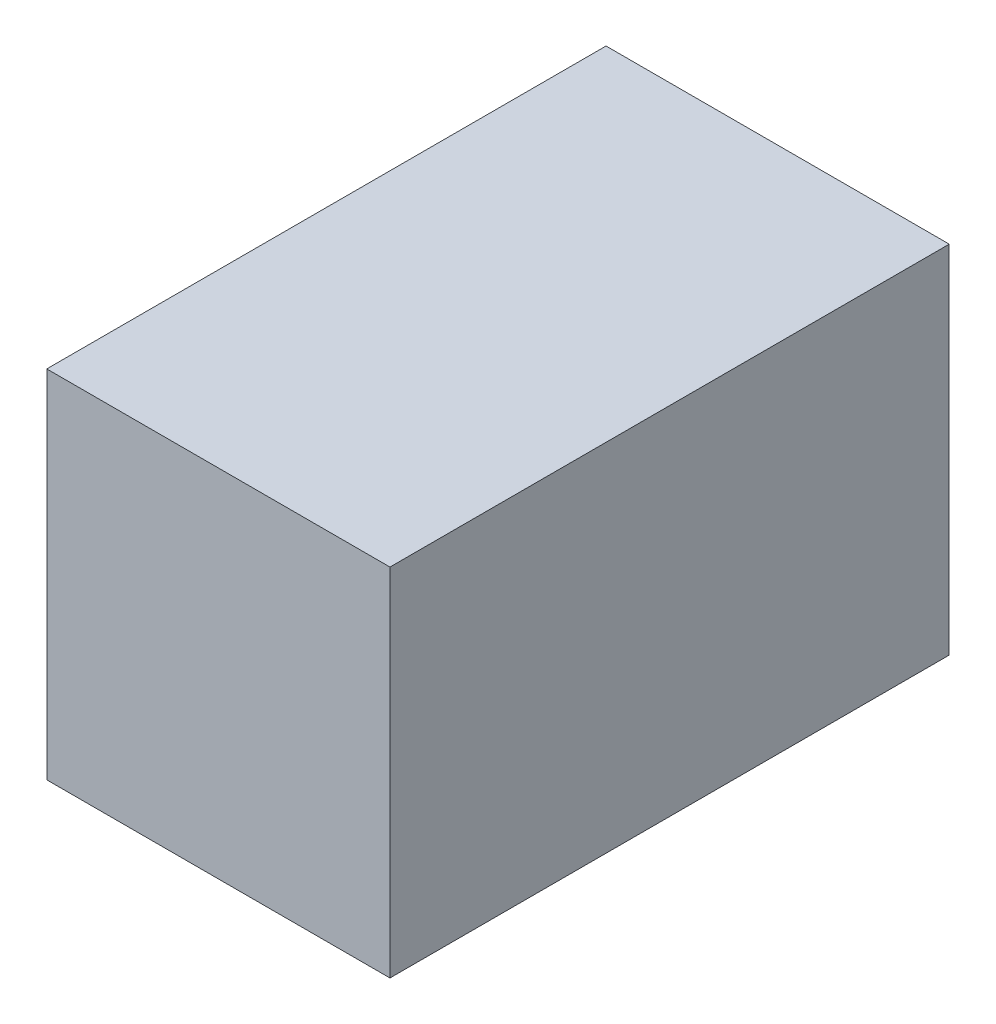
SolidWorks part; units mm, degrees
ref_plane "Front Plane" through (0, 0, 0) normal (0, 0, 1) x (1, 0, 0)
ref_plane "Top Plane" through (0, 0, 0) normal (0, 1, 0) x (1, 0, 0)
ref_plane "Right Plane" through (0, 0, 0) normal (1, 0, 0) x (0, 0, -1)
sketch "Sketch1" plane through (0, 0, 0) normal (0, 1, 0) x (1, 0, 0)
  line L1 (0, 0) -> (171.45, 0)
  line L2 (0, 0) -> (0, 279.4)
  line L3 (0, 279.4) -> (171.45, 279.4)
  line L4 (171.45, 0) -> (171.45, 279.4)
  dimension "D1" = 279.4
  dimension "D2" = 171.45
extrude "Boss-Extrude1" add sketch "Sketch1" along normal blind 177.8
